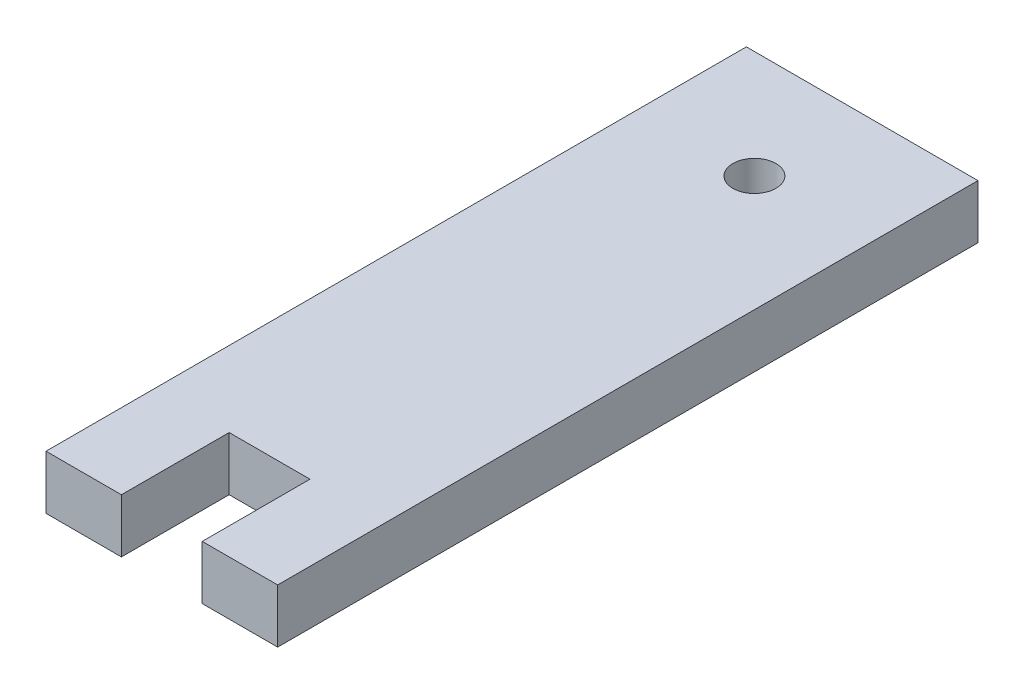
SolidWorks part; units mm, degrees
ref_plane "Front Plane" through (0, 0, 0) normal (0, 0, 1) x (1, 0, 0)
ref_plane "Top Plane" through (0, 0, 0) normal (0, 1, 0) x (1, 0, 0)
ref_plane "Right Plane" through (0, 0, 0) normal (1, 0, 0) x (0, 0, -1)
sketch "Sketch1" plane through (0, 0, 0) normal (0, 1, 0) x (1, 0, 0)
  line L0 (-3.75, -32.5) -> (3.75, -32.5) construction
  line L1 (-10.75, 32.5) -> (10.75, 32.5)
  line L2 (-10.75, 32.5) -> (-10.75, -32.5)
  line L3 (-10.75, -32.5) -> (-3.75, -32.5)
  line L4 (10.75, 32.5) -> (10.75, -32.5)
  line L5 (-10.75, 32.5) -> (10.75, -32.5) construction
  line L6 (-10.75, -32.5) -> (10.75, 32.5) construction
  line L7 (-3.75, -22.5) -> (3.75, -22.5)
  line L8 (-3.75, -22.5) -> (-3.75, -32.5)
  line L9 (-3.75, -32.5) -> (3.75, -32.5) construction
  line L10 (3.75, -22.5) -> (3.75, -32.5)
  line L11 (-3.75, -22.5) -> (3.75, -32.5) construction
  line L12 (-3.75, -32.5) -> (3.75, -22.5) construction
  line L13 (3.75, -32.5) -> (10.75, -32.5)
  circle A0 centre (0, 22.5) radius 2
  point P0 (0, 0)
  point P6 (0, -27.5)
  point P11 (0, 0)
  dimension "D6" = 4
  dimension "D1" = 65
  dimension "D2" = 21.5
  dimension "D3" = 7.5
  dimension "D4" = 10
  dimension "D5" = 10
extrude "Boss-Extrude1" add sketch "Sketch1" along normal blind 5
